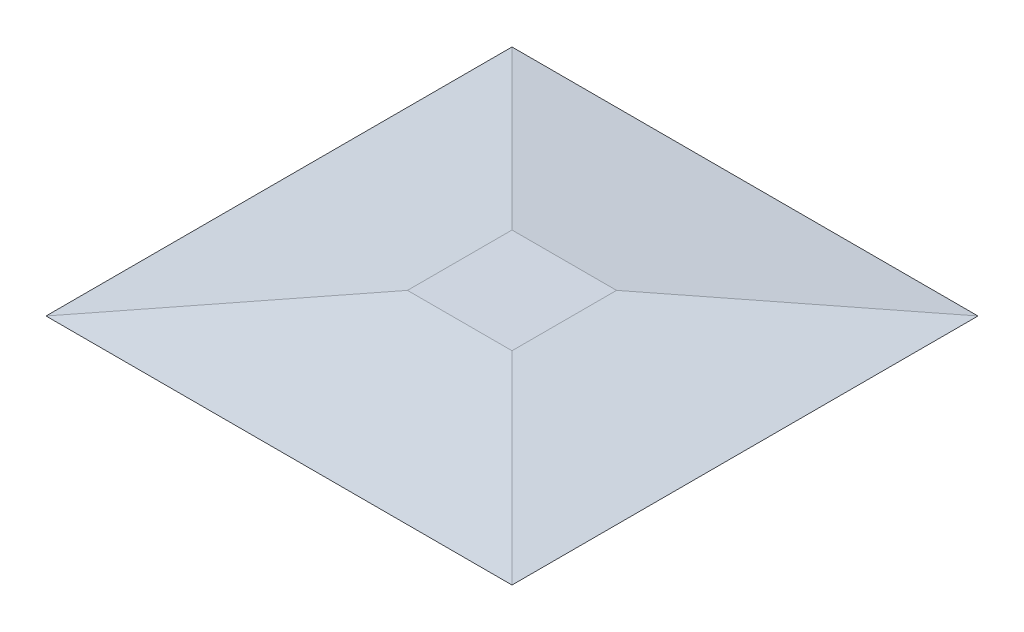
SolidWorks part; units mm, degrees
ref_plane "Alzado" through (0, 0, 0) normal (0, 0, 1) x (1, 0, 0)
ref_plane "Planta" through (0, 0, 0) normal (0, 1, 0) x (1, 0, 0)
ref_plane "Vista lateral" through (0, 0, 0) normal (1, 0, 0) x (0, 0, -1)
sketch "Croquis1" plane through (0, 0, 0) normal (0, 1, 0) x (1, 0, 0)
  line L1 (-38.718, -29.315) -> (14.622, -29.315)
  line L2 (-38.718, -29.315) -> (-38.718, 24.025)
  line L3 (-38.718, 24.025) -> (14.622, 24.025)
  line L4 (14.622, -29.315) -> (14.622, 24.025)
  dimension "D1" = 53.34
  dimension "D2" = 53.34
extrude "Saliente-Extruir1" add sketch "Croquis1" along normal blind 2.54 draft 83
